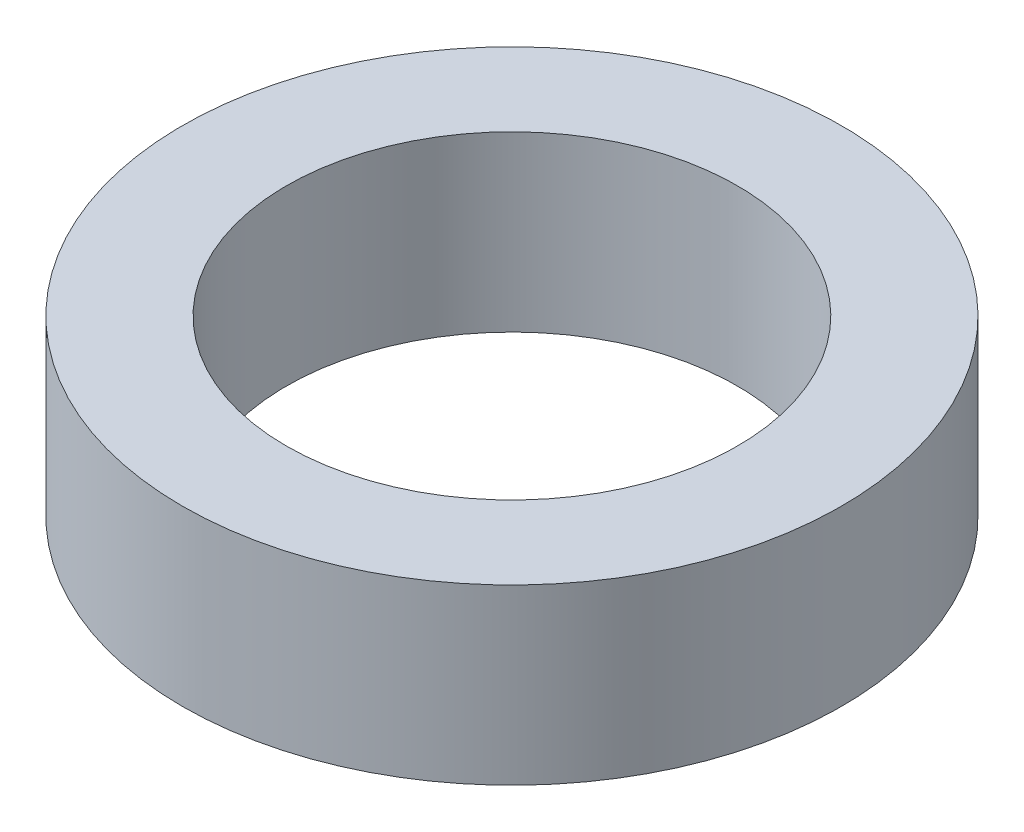
SolidWorks part; units mm, degrees
ref_plane "Front Plane" through (0, 0, 0) normal (0, 0, 1) x (1, 0, 0)
ref_plane "Top Plane" through (0, 0, 0) normal (0, 1, 0) x (1, 0, 0)
ref_plane "Right Plane" through (0, 0, 0) normal (1, 0, 0) x (0, 0, -1)
sketch "Sketch1" plane through (0, 0, 0) normal (0, 1, 0) x (1, 0, 0)
  line L0 (0, 1.9562) -> (0, -1.9562) construction
  circle A0 centre (0, 0) radius 12.065
  circle A1 centre (0, 0) radius 8.255
  dimension "D1" = 24.13
  dimension "D2" = 16.51
extrude "Boss-Extrude1" add sketch "Sketch1" along normal blind 6.35
